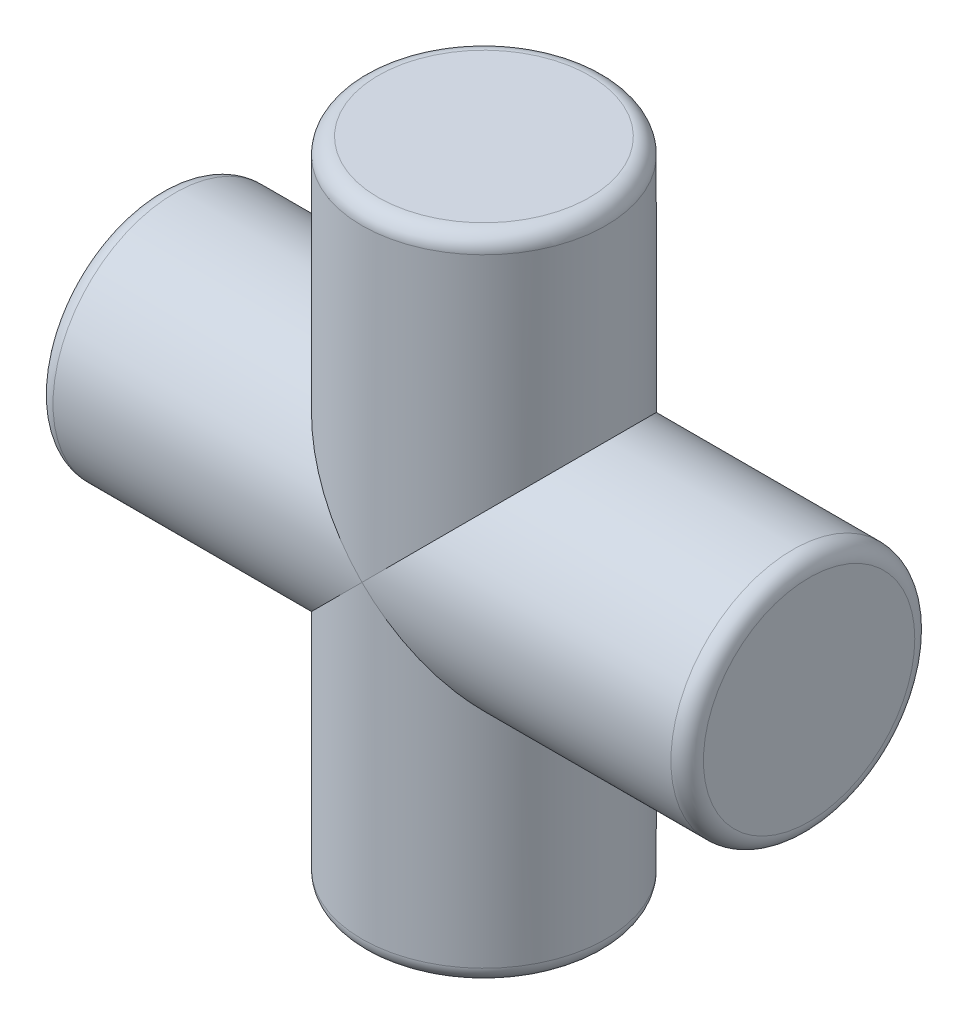
SolidWorks part; units mm, degrees
material "Alloy Steel"
ref_plane "Front Plane" through (0, 0, 0) normal (0, 0, 1) x (1, 0, 0)
ref_plane "Top Plane" through (0, 0, 0) normal (0, 1, 0) x (1, 0, 0)
ref_plane "Right Plane" through (0, 0, 0) normal (1, 0, 0) x (0, 0, -1)
sketch "Sketch1" plane through (0, 0, 0) normal (0, 1, 0) x (1, 0, 0)
  circle A0 centre (0, 0) radius 7.5
  dimension "D1" = 15
extrude "Boss-Extrude1" add sketch "Sketch1" along normal mid plane 40
sketch "Sketch2" plane through (0, 0, 0) normal (1, 0, 0) x (0, 0, -1)
  circle A0 centre (0, 0) radius 7.5
  dimension "D1" = 15
extrude "Boss-Extrude2" add sketch "Sketch2" along normal mid plane 40
fillet "Fillet1" radius 1 4 edges at (-20, 0, -7.5) (0, -20, 7.5) (20, 0, -7.5) (0, 20, 7.5)
